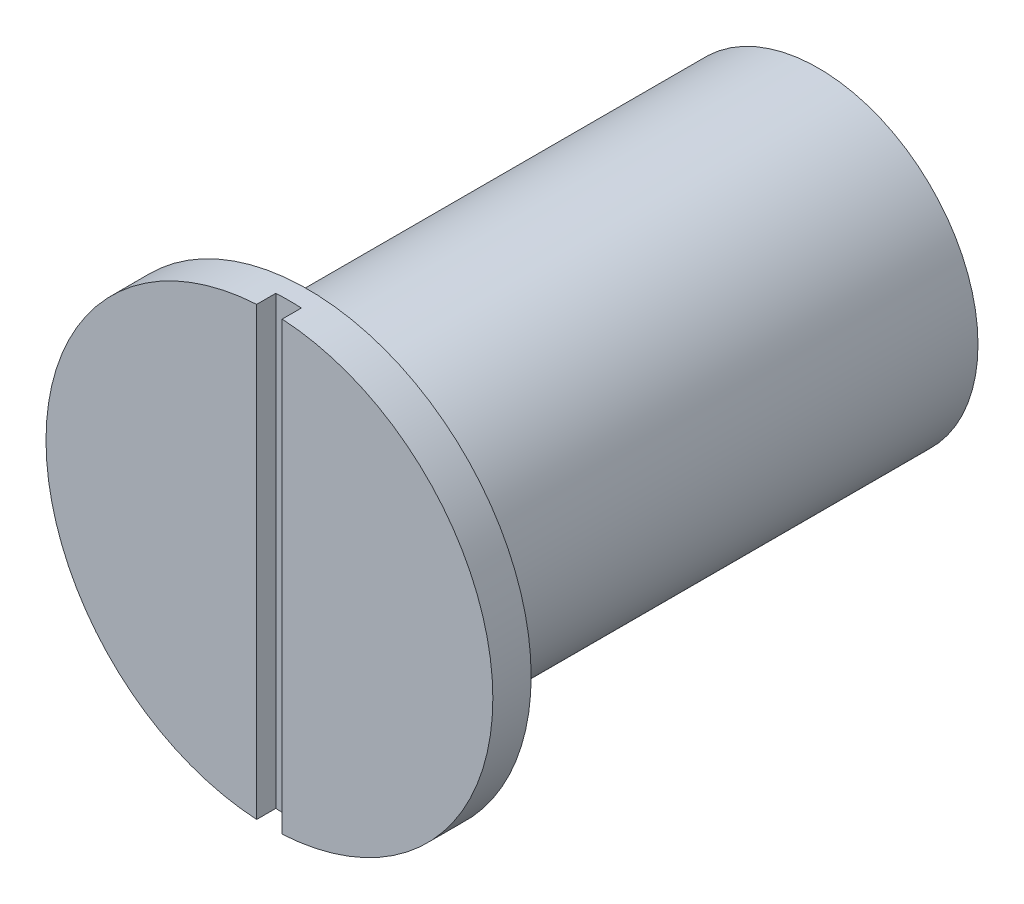
SolidWorks part; units mm, degrees
ref_plane "Alzado" through (0, 0, 0) normal (0, 0, 1) x (1, 0, 0)
ref_plane "Planta" through (0, 0, 0) normal (0, 1, 0) x (1, 0, 0)
ref_plane "Vista lateral" through (0, 0, 0) normal (1, 0, 0) x (0, 0, -1)
sketch "Croquis1" plane through (0, 0, 0) normal (0, 0, 1) x (1, 0, 0)
  circle A0 centre (0, 0) radius 1.75
  dimension "D1" = 3.5
extrude "Saliente-Extruir1" add sketch "Croquis1" along normal blind 0.3
sketch "Croquis2" plane through (0, 0, 0.3) normal (0, 0, 1) x (1, 0, 0)
  line L0 (0, 0) -> (0.1, 0) construction
  line L1 (0.1, 1.7471) -> (0.1, -1.7471)
  line L2 (0, 0) -> (0, 0.4498) construction
  line L3 (-0.1, 1.7471) -> (-0.1, -1.7471)
  circle A0 centre (0, 0) radius 1.75 construction
  arc A1 (-0.1, -1.7471) -> (0.1, -1.7471) centre (0, 0) ccw
  arc A2 (0.1, 1.7471) -> (-0.1, 1.7471) centre (0, 0) ccw
  dimension "D1" = 0.1
extrude "Cortar-Extruir1" cut sketch "Croquis2" against normal blind 0.15
sketch "Croquis3" plane through (0, 0, 0) normal (0, 0, -1) x (-1, 0, 0)
  circle A0 centre (0, 0) radius 1.25
  dimension "D1" = 2.5
extrude "Saliente-Extruir2" add sketch "Croquis3" along normal blind 4
fillet "Redondeo1" radius 0.1 1 edges at (1.25, 0, 0)
